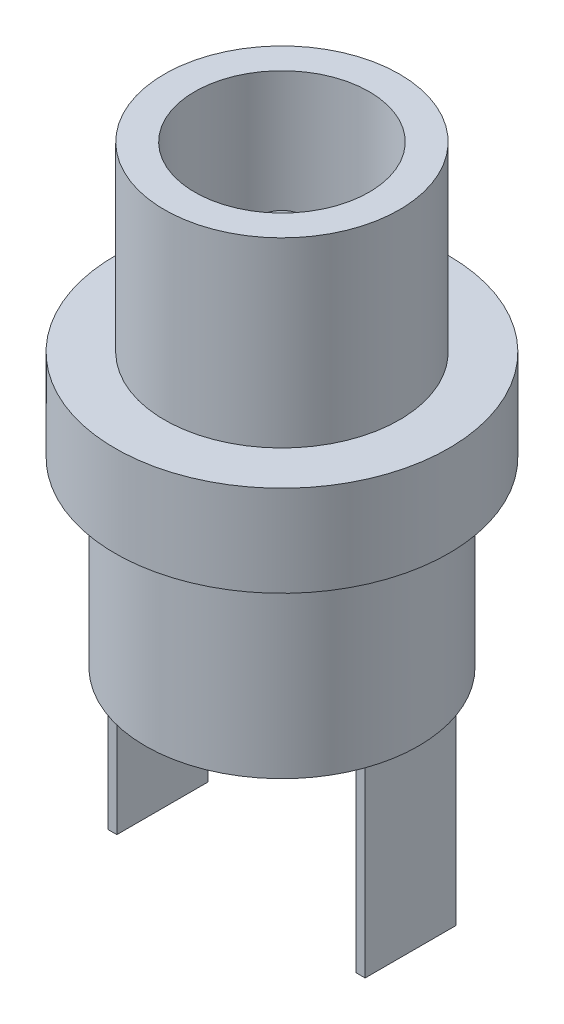
SolidWorks part; units mm, degrees
material "1023 Kohlenstoffstahlblech (SS)"
ref_plane "Ebene vorne" through (0, 0, 0) normal (0, 0, 1) x (1, 0, 0)
ref_plane "Ebene oben" through (0, 0, 0) normal (0, 1, 0) x (1, 0, 0)
ref_plane "Ebene rechts" through (0, 0, 0) normal (1, 0, 0) x (0, 0, -1)
sketch "Skizze1" plane through (0, 0, 0) normal (0, 0, 1) x (1, 0, 0)
  line L0 (0, 0) -> (-3.875, 0) construction
  line L1 (-3.875, 0) -> (-3.875, -6)
  line L2 (-3.875, -6) -> (-5.5, -6)
  line L3 (-5.5, -6) -> (-5.5, -9)
  line L4 (-5.5, -9) -> (-4.5, -9)
  line L5 (-4.5, -9) -> (-4.5, -15)
  line L6 (-4.5, -15) -> (0, -15)
  line L7 (0, -15) -> (0, 0) construction
  line L8 (0, -15) -> (0, -2.3)
  line L9 (0, -2.3) -> (-1, -2.3)
  line L10 (-1, -2.3) -> (-1, -10)
  line L11 (-1, -10) -> (-2.875, -10)
  line L12 (-2.875, -10) -> (-2.875, 0)
  line L13 (-2.875, 0) -> (-3.875, 0)
  point P13 (0, 0)
  point P16 (-3.9312, 0)
  dimension "D1" = 6
  dimension "D2" = 3
  dimension "D3" = 6
  dimension "D4" = 3.875
  dimension "D5" = 5.5
  dimension "D6" = 4.5
  dimension "D7" = 1
  dimension "D8" = 1
  dimension "D9" = 2.3
  dimension "D10" = 10
revolve "Rotation1" add sketch "Skizze1" angle 360 about L7
sketch "Skizze2" plane through (0, -15, 0) normal (0, -1, 0) x (1, 0, 0)
  line L0 (-3.9426, 0) -> (0, 0) construction
  line L1 (-4.2426, 1.5) -> (-3.9426, 1.5)
  line L2 (-4.2426, 1.5) -> (-4.2426, -1.5)
  line L3 (-4.2426, -1.5) -> (-3.9426, -1.5)
  line L4 (-3.9426, 1.5) -> (-3.9426, -1.5)
  line L5 (3.9426, 1.5) -> (4.2426, 1.5)
  line L6 (3.9426, 1.5) -> (3.9426, -1.5)
  line L7 (3.9426, -1.5) -> (4.2426, -1.5)
  line L8 (4.2426, 1.5) -> (4.2426, -1.5)
  line L9 (1.5, -3.9426) -> (-1.5, -3.9426)
  line L10 (1.5, -3.9426) -> (1.5, -4.2426)
  line L11 (1.5, -4.2426) -> (-1.5, -4.2426)
  line L12 (-1.5, -3.9426) -> (-1.5, -4.2426)
  line L13 (0, 0) -> (3.9426, 0) construction
  line L14 (0, 0) -> (0, -3.9426) construction
  circle A0 centre (0, 0) radius 4.5 construction
  point P17 (0, 0)
  dimension "D1" = 3
  dimension "D2" = 0.3
  dimension "D3" = 0.3
  dimension "D4" = 3
  dimension "D5" = 3
  dimension "D6" = 0.3
extrude "Aufsatz-Linear austragen1" add sketch "Skizze2" along normal blind 6
fillet "Verrundung1" radius 0.75 1 edges at (0, -2.3, -1)
